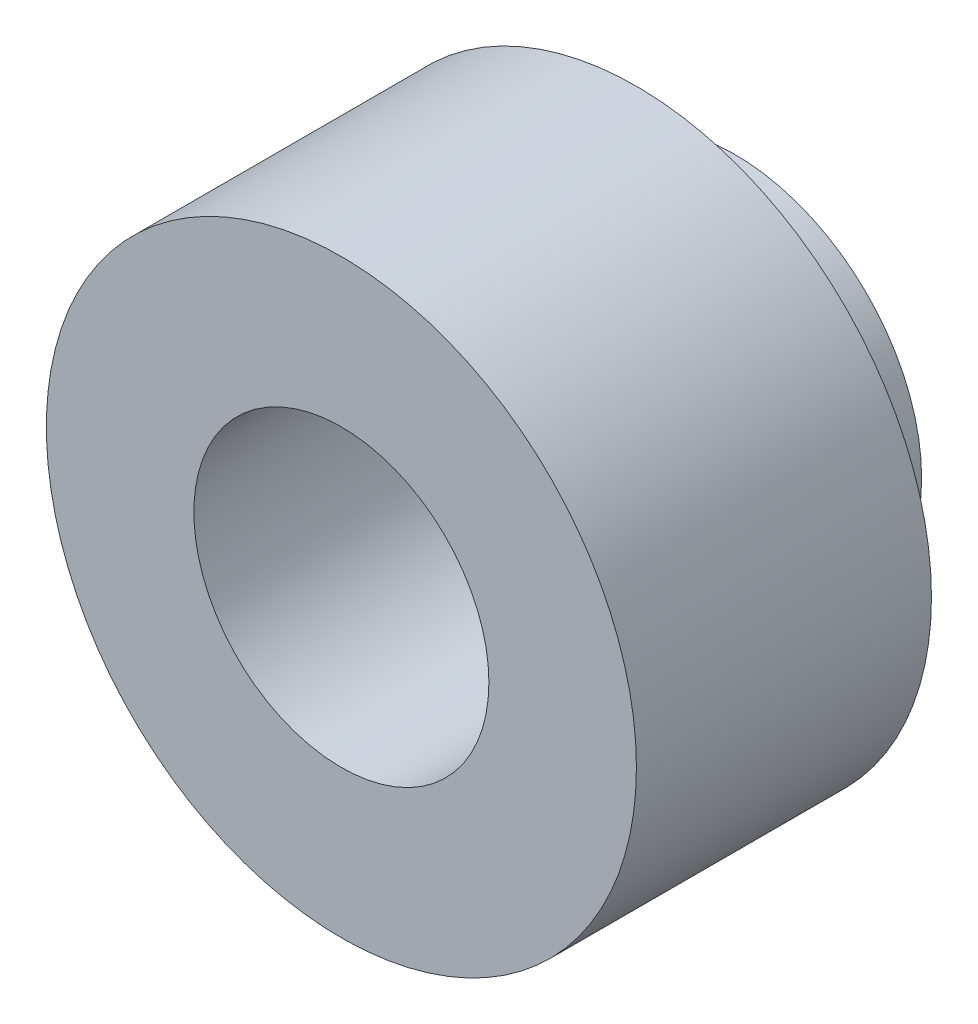
SolidWorks part; units mm, degrees
ref_plane "Front Plane" through (0, 0, 0) normal (0, 0, 1) x (1, 0, 0)
ref_plane "Top Plane" through (0, 0, 0) normal (0, 1, 0) x (1, 0, 0)
ref_plane "Right Plane" through (0, 0, 0) normal (1, 0, 0) x (0, 0, -1)
sketch "Sketch1" plane through (0, 0, 0) normal (0, 1, 0) x (1, 0, 0)
  line L0 (2.375, 5) -> (2.375, 3.75)
  line L1 (1.875, 0) -> (3.75, 0)
  line L2 (1.875, 0) -> (1.875, 5)
  line L3 (1.875, 5) -> (2.375, 5)
  line L4 (3.75, 0) -> (3.75, 3.75)
  line L5 (2.375, 3.75) -> (3.75, 3.75)
  line L6 (0, 0) -> (0, 12.5211) construction
  dimension "D1" = 1.875
  dimension "D2" = 3.75
  dimension "D3" = 0.5
  dimension "D4" = 1.25
  dimension "D5" = 3.75
revolve "Revolve1" add sketch "Sketch1" angle 360 about L6
